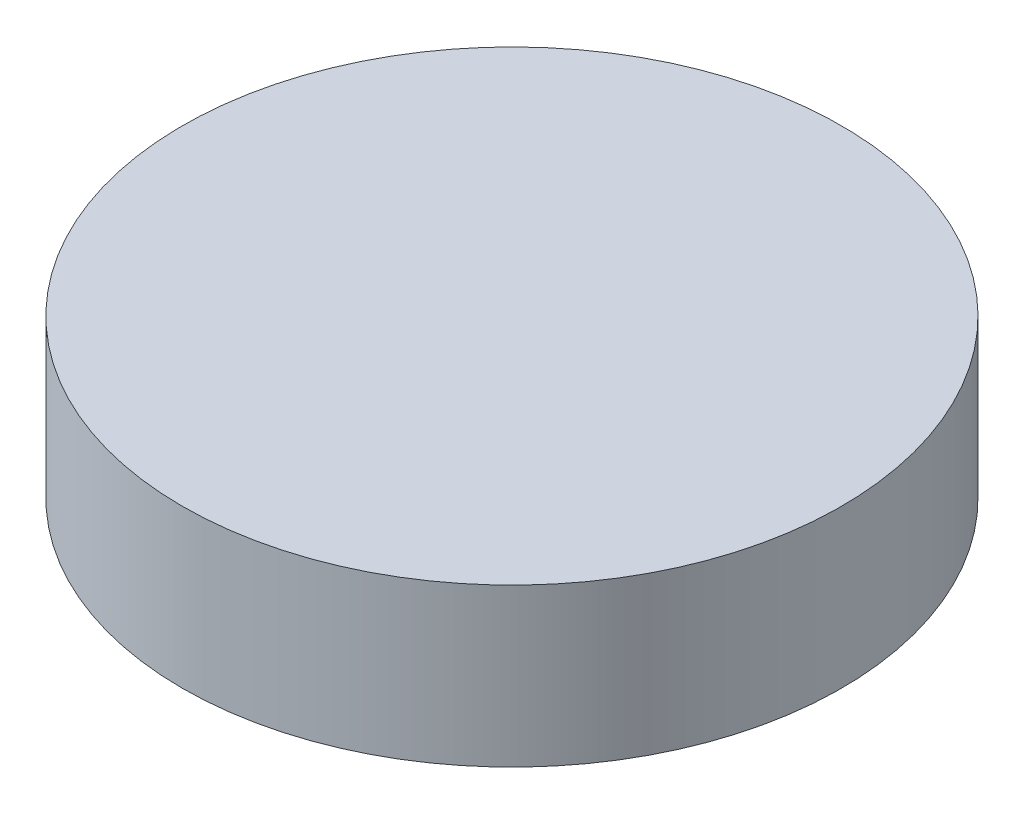
SolidWorks part; units mm, degrees
ref_plane "Front" through (0, 0, 0) normal (0, 0, 1) x (1, 0, 0)
ref_plane "Top" through (0, 0, 0) normal (0, 1, 0) x (1, 0, 0)
ref_plane "Right" through (0, 0, 0) normal (1, 0, 0) x (0, 0, -1)
sketch "Sketch1" plane through (0, 0, 0) normal (0, 1, 0) x (1, 0, 0)
  circle A0 centre (0, 0) radius 6.6378
  dimension "D1" = 13.2756
extrude "Boss-Extrude1" add sketch "Sketch1" along normal blind 3.175
